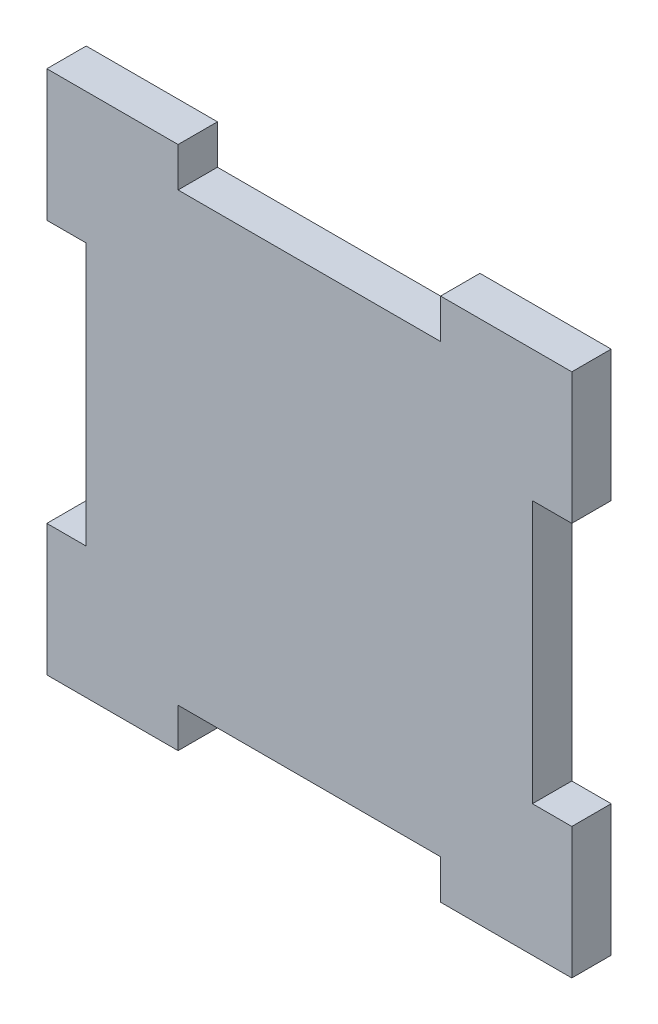
SolidWorks part; units mm, degrees
ref_plane "Alzado" through (0, 0, 0) normal (0, 0, 1) x (1, 0, 0)
ref_plane "Planta" through (0, 0, 0) normal (0, 1, 0) x (1, 0, 0)
ref_plane "Vista lateral" through (0, 0, 0) normal (1, 0, 0) x (0, 0, -1)
sketch "Croquis1" plane through (0, 0, 0) normal (0, 0, 1) x (1, 0, 0)
  line L0 (-42.4407, -22.8975) -> (-42.4407, -25.8975)
  line L1 (-42.4407, -25.8975) -> (-22.4407, -25.8975)
  line L2 (-22.4407, -22.8975) -> (-22.4407, -25.8975)
  line L3 (-42.4407, -22.8975) -> (-52.4407, -22.8975)
  line L4 (-22.4407, -22.8975) -> (-12.4407, -22.8975)
  line L5 (-22.4407, -62.8975) -> (-12.4407, -62.8975)
  line L6 (-42.4407, -62.8975) -> (-52.4407, -62.8975)
  line L7 (-22.4407, -62.8975) -> (-22.4407, -59.8975)
  line L8 (-42.4407, -59.8975) -> (-22.4407, -59.8975)
  line L9 (-42.4407, -62.8975) -> (-42.4407, -59.8975)
  line L10 (-52.4407, -32.8975) -> (-52.4407, -22.8975)
  line L11 (-52.4407, -32.8975) -> (-49.4407, -32.8975)
  line L12 (-52.4407, -52.8975) -> (-49.4407, -52.8975)
  line L13 (-49.4407, -32.8975) -> (-49.4407, -52.8975)
  line L14 (-52.4407, -52.8975) -> (-52.4407, -62.8975)
  line L15 (-32.4407, -7.0197) -> (-32.4407, -69.3136) construction
  line L16 (-12.4407, -32.8975) -> (-12.4407, -22.8975)
  line L17 (-12.4407, -32.8975) -> (-15.4407, -32.8975)
  line L18 (-15.4407, -32.8975) -> (-15.4407, -52.8975)
  line L19 (-12.4407, -52.8975) -> (-15.4407, -52.8975)
  line L20 (-12.4407, -52.8975) -> (-12.4407, -62.8975)
  dimension "D1" = 40
  dimension "D2" = 20
  dimension "D3" = 10
  dimension "D4" = 3
  dimension "D5" = 20
  dimension "D6" = 10
  dimension "D7" = 10
  dimension "D8" = 10
extrude "Saliente-Extruir1" add sketch "Croquis1" along normal blind 3
